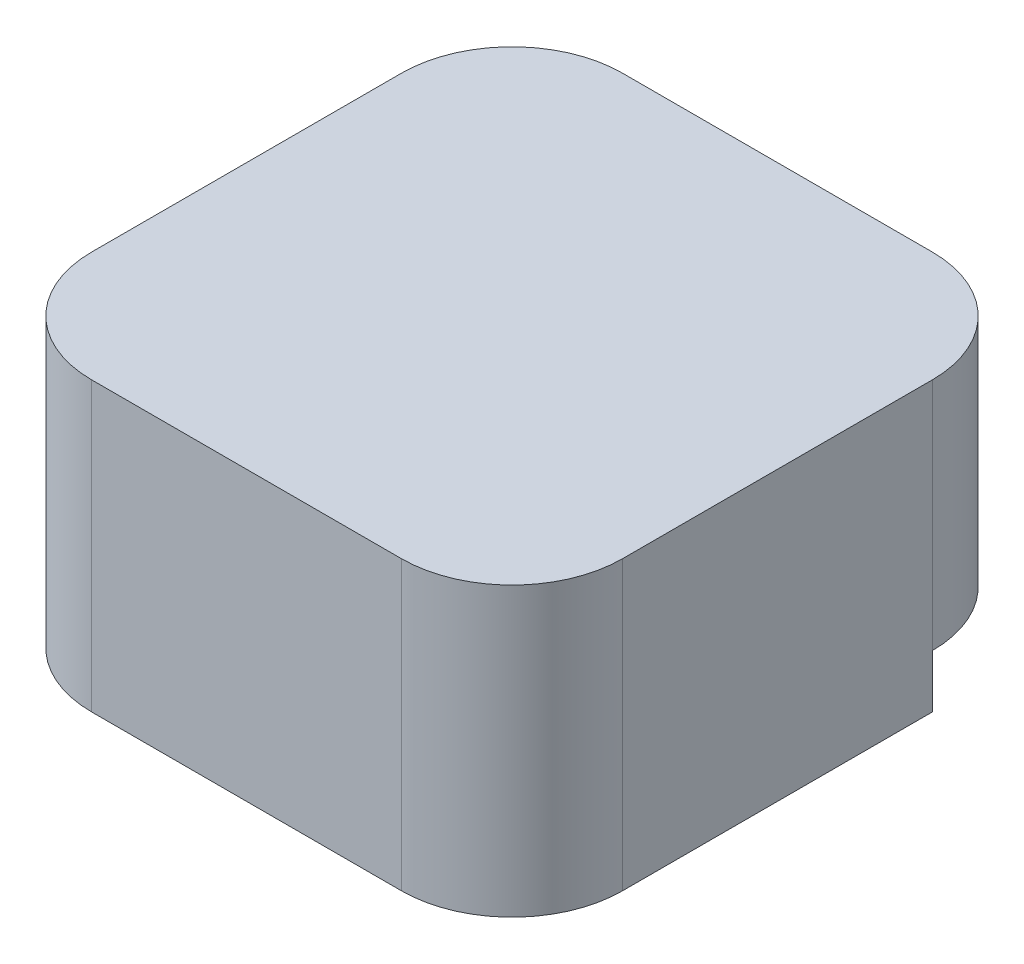
SolidWorks part; units mm, degrees
ref_plane "Přední rovina" through (0, 0, 0) normal (0, 0, 1) x (1, 0, 0)
ref_plane "Horní rovina" through (0, 0, 0) normal (0, 1, 0) x (1, 0, 0)
ref_plane "Pravá rovina" through (0, 0, 0) normal (1, 0, 0) x (0, 0, -1)
sketch "Skica1" plane through (0, 0, 0) normal (0, 1, 0) x (1, 0, 0)
  line L1 (0, 0) -> (12, 0)
  line L2 (0, 0) -> (0, 12)
  line L3 (0, 12) -> (12, 12)
  line L4 (12, 0) -> (12, 12)
  line L5 (3.95, 3.95) -> (8.05, 3.95)
  line L6 (3.95, 3.95) -> (3.95, 8.05)
  line L7 (3.95, 8.05) -> (8.05, 8.05)
  line L8 (8.05, 3.95) -> (8.05, 8.05)
  point P9 (8.05, 6)
  point P10 (12, 6)
  point P11 (6, 12)
  point P12 (6, 8.05)
  dimension "D1" = 4.1
  dimension "D2" = 4.1
  dimension "D3" = 12
  dimension "D4" = 12
extrude "Přidat vysunutím1" add sketch "Skica1" along normal blind 2.5
sketch "Skica2" plane through (0, 2.5, 0) normal (0, 1, 0) x (1, 0, 0)
  line L1 (0, 0) -> (12, 0)
  line L2 (0, 0) -> (0, 12)
  line L3 (0, 12) -> (12, 12)
  line L4 (12, 0) -> (12, 12)
extrude "Přidat vysunutím2" add sketch "Skica2" along normal blind 4
fillet "Zaoblit1" radius 2.5 4 edges at (12, 3.25, -12) (0, 3.25, -12) (0, 3.25, 0) (12, 3.25, 0)
sketch "Skica3" plane through (12, 0, 0) normal (1, 0, 0) x (0, 0, -1)
  line L1 (9.5, 0) -> (12.5, 0)
  line L2 (9.5, 0) -> (9.5, 1.2)
  line L3 (9.5, 1.2) -> (12.5, 1.2)
  line L4 (12.5, 0) -> (12.5, 1.2)
  dimension "D1" = 3
  dimension "D2" = 1.2
extrude "Odebrat vysunutím1" cut sketch "Skica3" against normal through all
